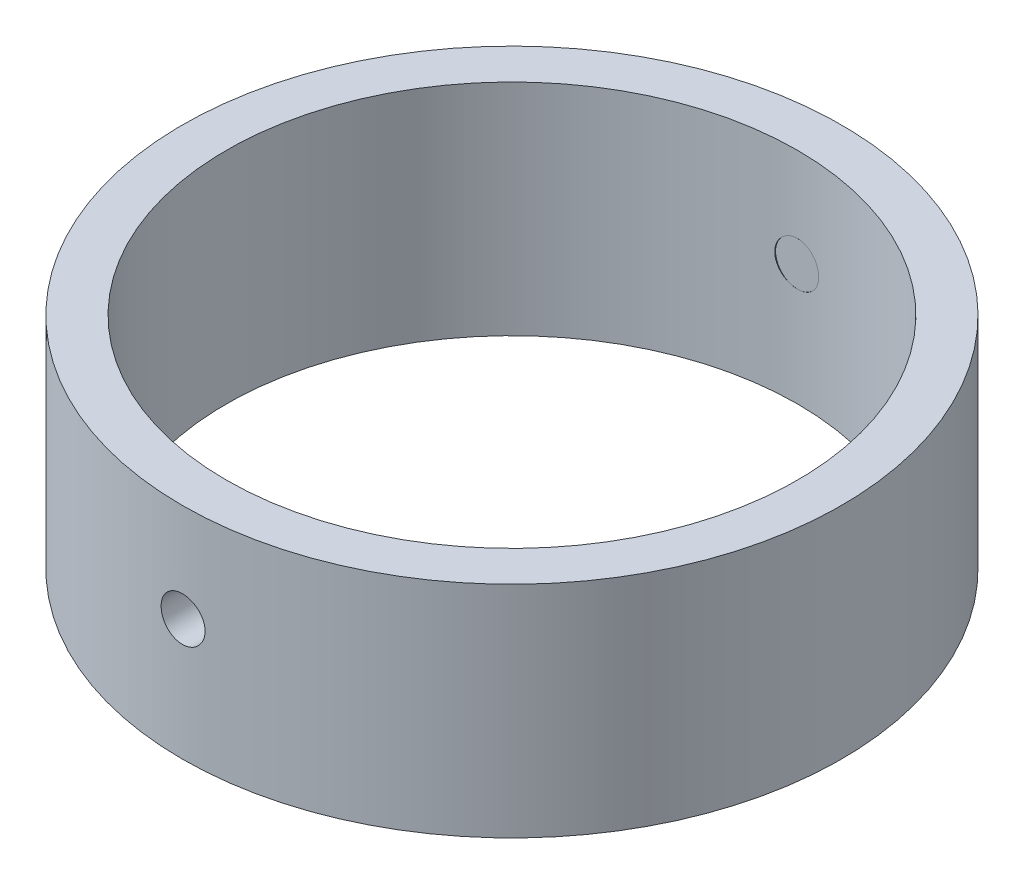
SolidWorks part; units mm, degrees
ref_plane "前视基准面" through (0, 0, 0) normal (0, 0, 1) x (1, 0, 0)
ref_plane "上视基准面" through (0, 0, 0) normal (0, 1, 0) x (1, 0, 0)
ref_plane "右视基准面" through (0, 0, 0) normal (1, 0, 0) x (0, 0, -1)
sketch "草图1" plane through (0, 0, 0) normal (0, 1, 0) x (1, 0, 0)
  circle A0 centre (0, 0) radius 13
  circle A1 centre (0, 0) radius 15
  dimension "D1" = 30
  dimension "D2" = 26
extrude "凸台-拉伸1" add sketch "草图1" along normal blind 10
ref_plane "基准面1" through (0, 0, -13) normal (0, 0, -1) x (-1, 0, 0)
sketch "草图2" plane through (0, 0, -13) normal (0, 0, -1) x (-1, 0, 0)
  circle A0 centre (0, 5.523) radius 1
  dimension "D1" = 2
extrude "切除-拉伸1" cut sketch "草图2" against normal through all
